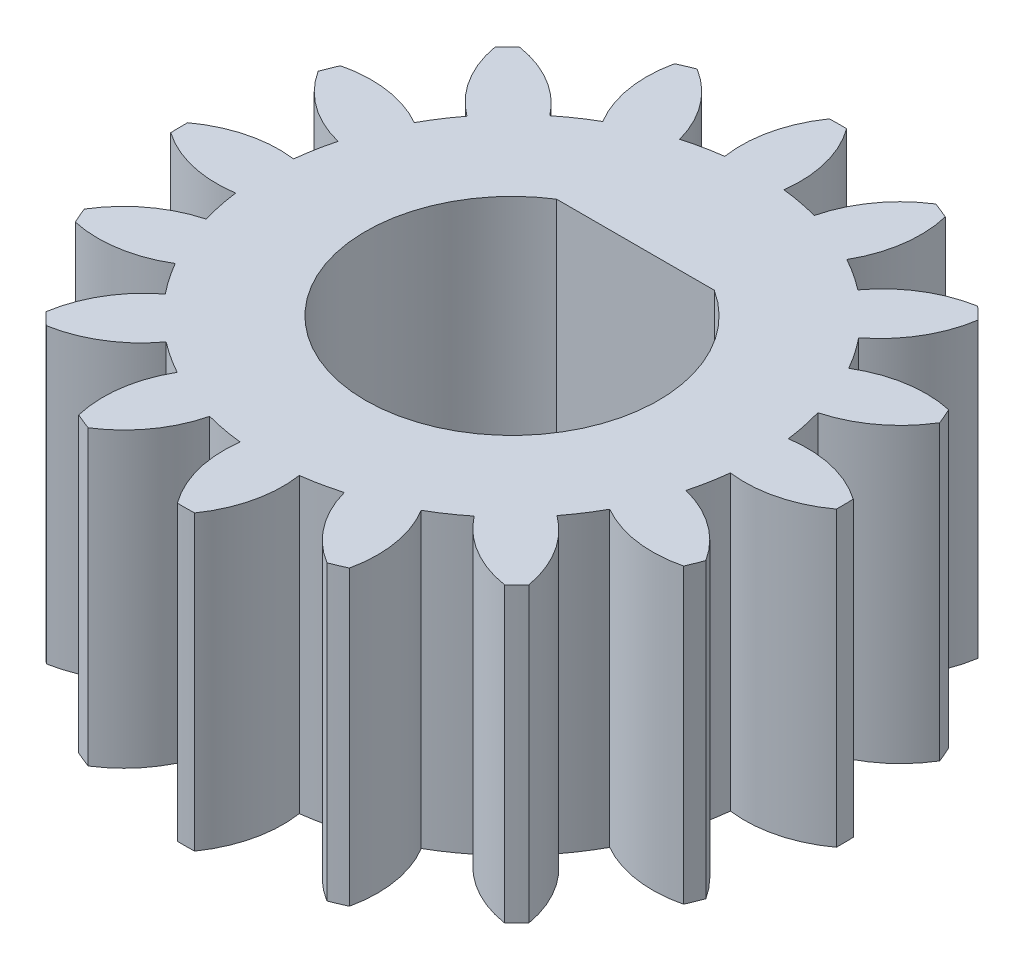
SolidWorks part; units mm, degrees
ref_plane "Front Plane" through (0, 0, 0) normal (0, 0, 1) x (1, 0, 0)
ref_plane "Top Plane" through (0, 0, 0) normal (0, 1, 0) x (1, 0, 0)
ref_plane "Right Plane" through (0, 0, 0) normal (1, 0, 0) x (0, 0, -1)
sketch "Sketch1" plane through (0, 0, 0) normal (0, 1, 0) x (1, 0, 0)
  line L0 (9.9611, -7.2541) -> (13.3816, -7.2541)
  line L1 (11.6714, -7.2541) -> (11.6714, -13.1041) construction
  arc A0 (9.1012, -14.6175) -> (8.8346, -16.4854) centre (11.3025, -15.8847) ccw
  arc A1 (8.8346, -16.4854) -> (9.1792, -16.624) centre (11.6714, -9.9291) ccw
  arc A2 (9.1792, -16.624) -> (10.28, -15.0916) centre (7.8143, -14.4819) ccw
  arc A3 (10.28, -15.0916) -> (11.091, -15.2442) centre (11.6714, -9.9291) ccw
  arc A4 (11.091, -15.2442) -> (11.5595, -17.072) centre (13.6097, -15.5725) ccw
  arc A5 (11.5595, -17.072) -> (11.9309, -17.0681) centre (11.6714, -9.9291) ccw
  arc A6 (11.9309, -17.0681) -> (12.3615, -15.2311) centre (9.8502, -15.6114) ccw
  arc A7 (12.3615, -15.2311) -> (13.1692, -15.0617) centre (11.6714, -9.9291) ccw
  arc A8 (13.1692, -15.0617) -> (14.3015, -16.571) centre (15.6218, -14.4012) ccw
  arc A9 (14.3015, -16.571) -> (14.6432, -16.4254) centre (11.6714, -9.9291) ccw
  arc A10 (14.6432, -16.4254) -> (14.338, -14.5634) centre (12.1633, -15.8758) ccw
  arc A11 (14.338, -14.5634) -> (15.0194, -14.0978) centre (11.6714, -9.9291) ccw
  arc A12 (15.0194, -14.0978) -> (16.643, -15.059) centre (17.0325, -12.549) ccw
  arc A13 (16.643, -15.059) -> (16.903, -14.7936) centre (11.6714, -9.9291) ccw
  arc A14 (16.903, -14.7936) -> (15.9084, -13.1901) centre (14.4016, -15.2349) ccw
  arc A15 (15.9084, -13.1901) -> (16.3598, -12.4993) centre (11.6714, -9.9291) ccw
  arc A16 (16.3598, -12.4993) -> (18.2277, -12.7659) centre (17.627, -10.298) ccw
  arc A17 (18.2277, -12.7659) -> (18.3663, -12.4213) centre (11.6714, -9.9291) ccw
  arc A18 (18.3663, -12.4213) -> (16.8339, -11.3205) centre (16.2242, -13.7862) ccw
  arc A19 (16.8339, -11.3205) -> (16.9865, -10.5094) centre (11.6714, -9.9291) ccw
  arc A20 (16.9865, -10.5094) -> (18.8143, -10.041) centre (17.3148, -7.9908) ccw
  arc A21 (18.8143, -10.041) -> (18.8104, -9.6695) centre (11.6714, -9.9291) ccw
  arc A22 (18.8104, -9.6695) -> (16.9734, -9.2389) centre (17.3537, -11.7503) ccw
  arc A23 (16.9734, -9.2389) -> (16.804, -8.4313) centre (11.6714, -9.9291) ccw
  arc A24 (16.804, -8.4313) -> (18.3133, -7.299) centre (16.1435, -5.9786) ccw
  arc A25 (18.3133, -7.299) -> (18.1677, -6.9573) centre (11.6714, -9.9291) ccw
  arc A26 (18.1677, -6.9573) -> (16.3057, -7.2625) centre (17.6181, -9.4371) ccw
  arc A27 (16.3057, -7.2625) -> (15.8401, -6.5811) centre (11.6714, -9.9291) ccw
  arc A28 (15.8401, -6.5811) -> (16.8013, -4.9574) centre (14.2913, -4.568) ccw
  arc A29 (16.8013, -4.9574) -> (16.5359, -4.6975) centre (11.6714, -9.9291) ccw
  arc A30 (16.5359, -4.6975) -> (14.9324, -5.692) centre (16.9772, -7.1989) ccw
  arc A31 (14.9324, -5.692) -> (14.2416, -5.2407) centre (11.6714, -9.9291) ccw
  arc A32 (14.2416, -5.2407) -> (14.5082, -3.3727) centre (12.0403, -3.9734) ccw
  arc A33 (14.5082, -3.3727) -> (14.1636, -3.2342) centre (11.6714, -9.9291) ccw
  arc A34 (14.1636, -3.2342) -> (13.0628, -4.7666) centre (15.5285, -5.3763) ccw
  arc A35 (13.0628, -4.7666) -> (12.2517, -4.614) centre (11.6714, -9.9291) ccw
  arc A36 (12.2517, -4.614) -> (11.7833, -2.7862) centre (9.7331, -4.2856) ccw
  arc A37 (11.7833, -2.7862) -> (11.4118, -2.79) centre (11.6714, -9.9291) ccw
  arc A38 (11.4118, -2.79) -> (10.9812, -4.6271) centre (13.4926, -4.2468) ccw
  arc A39 (10.9812, -4.6271) -> (10.1736, -4.7965) centre (11.6714, -9.9291) ccw
  arc A40 (10.1736, -4.7965) -> (9.0413, -3.2871) centre (7.7209, -5.457) ccw
  arc A41 (9.0413, -3.2871) -> (8.6996, -3.4328) centre (11.6714, -9.9291) ccw
  arc A42 (8.6996, -3.4328) -> (9.0048, -5.2948) centre (11.1794, -3.9823) ccw
  arc A43 (9.0048, -5.2948) -> (8.3234, -5.7604) centre (11.6714, -9.9291) ccw
  arc A44 (8.3234, -5.7604) -> (6.6997, -4.7992) centre (6.3103, -7.3092) ccw
  arc A45 (6.6997, -4.7992) -> (6.4398, -5.0645) centre (11.6714, -9.9291) ccw
  arc A46 (6.4398, -5.0645) -> (7.4343, -6.668) centre (8.9412, -4.6233) ccw
  arc A47 (7.4343, -6.668) -> (6.983, -7.3589) centre (11.6714, -9.9291) ccw
  arc A48 (6.983, -7.3589) -> (5.115, -7.0923) centre (5.7157, -9.5602) ccw
  arc A49 (5.115, -7.0923) -> (4.9764, -7.4369) centre (11.6714, -9.9291) ccw
  arc A50 (4.9764, -7.4369) -> (6.5089, -8.5377) centre (7.1185, -6.072) ccw
  arc A51 (6.5089, -8.5377) -> (6.3563, -9.3487) centre (11.6714, -9.9291) ccw
  arc A52 (6.3563, -9.3487) -> (4.5285, -9.8172) centre (6.0279, -11.8674) ccw
  arc A53 (4.5285, -9.8172) -> (4.5323, -10.1886) centre (11.6714, -9.9291) ccw
  arc A54 (4.5323, -10.1886) -> (6.3694, -10.6192) centre (5.9891, -8.1079) ccw
  arc A55 (6.3694, -10.6192) -> (6.5388, -11.4269) centre (11.6714, -9.9291) ccw
  arc A56 (6.5388, -11.4269) -> (5.0294, -12.5592) centre (7.1993, -13.8795) ccw
  arc A57 (5.0294, -12.5592) -> (5.1751, -12.9009) centre (11.6714, -9.9291) ccw
  arc A58 (5.1751, -12.9009) -> (7.0371, -12.5957) centre (5.7246, -10.421) ccw
  arc A59 (7.0371, -12.5957) -> (7.5027, -13.2771) centre (11.6714, -9.9291) ccw
  arc A60 (7.5027, -13.2771) -> (6.5415, -14.9007) centre (9.0515, -15.2902) ccw
  arc A61 (6.5415, -14.9007) -> (6.8068, -15.1607) centre (11.6714, -9.9291) ccw
  arc A62 (6.8068, -15.1607) -> (8.4103, -14.1661) centre (6.3656, -12.6593) ccw
  arc A63 (8.4103, -14.1661) -> (9.1012, -14.6175) centre (11.6714, -9.9291) ccw
  arc A64 (9.9611, -7.2541) -> (13.3816, -7.2541) centre (11.6714, -9.9291) ccw
  dimension "D2" = 6.35
  dimension "D1" = 7.7014
  dimension "D3" = 5.85
extrude "Boss-Extrude1" add sketch "Sketch1" along normal blind 6.35
